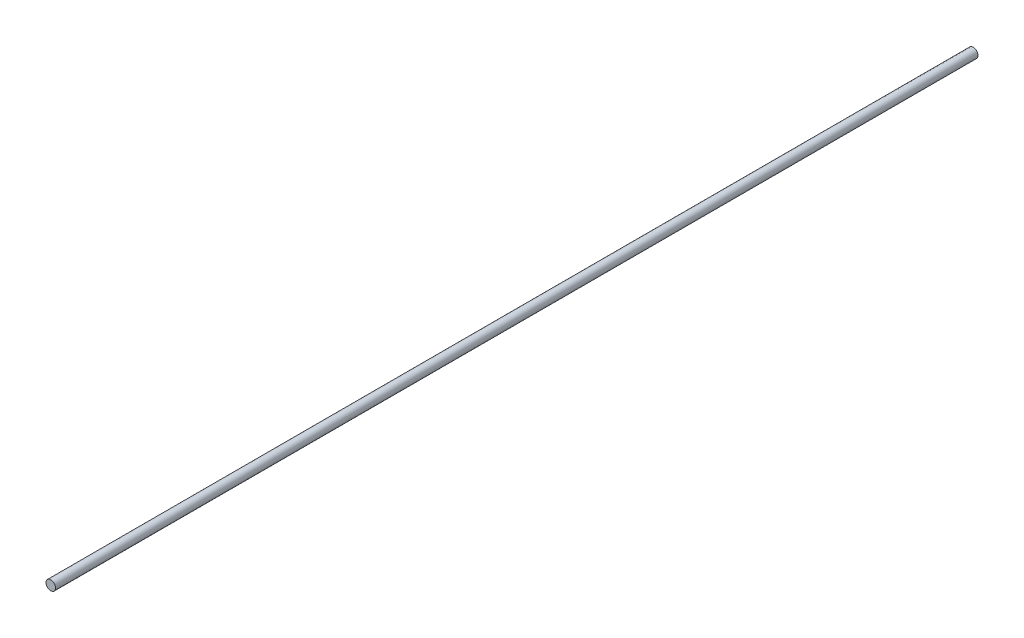
SolidWorks part; units mm, degrees
material "Pine"
ref_plane "Front Plane" through (0, 0, 0) normal (0, 0, 1) x (1, 0, 0)
ref_plane "Top Plane" through (0, 0, 0) normal (0, 1, 0) x (1, 0, 0)
ref_plane "Right Plane" through (0, 0, 0) normal (1, 0, 0) x (0, 0, -1)
sketch "Sketch1" plane through (0, 0, 0) normal (0, 0, 1) x (1, 0, 0)
  circle A0 centre (0, 0) radius 3.175
  dimension "D1" = 6.35
extrude "Boss-Extrude1" add sketch "Sketch1" along normal mid plane 614.68
